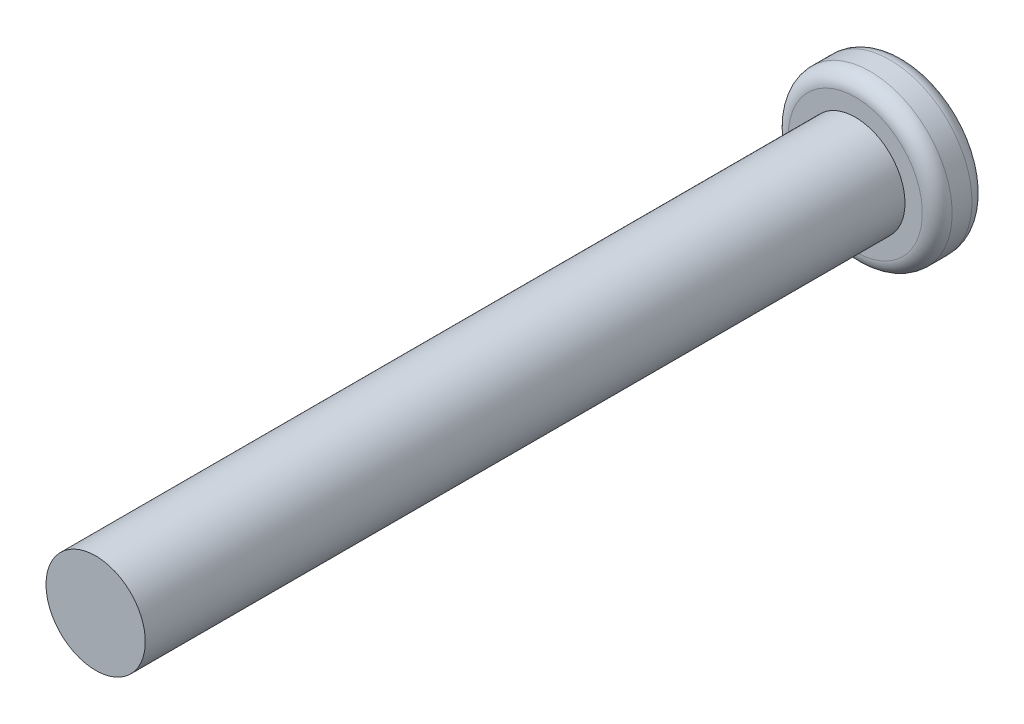
SolidWorks part; units mm, degrees
ref_plane "Front Plane" through (0, 0, 0) normal (0, 0, 1) x (1, 0, 0)
ref_plane "Top Plane" through (0, 0, 0) normal (0, 1, 0) x (1, 0, 0)
ref_plane "Right Plane" through (0, 0, 0) normal (1, 0, 0) x (0, 0, -1)
ref_plane "Plane1" through (0, 0, 0) normal (0, -1, 0) x (1, 0, 0)
sketch "Sketch1" plane through (0, 0, 0) normal (0, -1, 0) x (1, 0, 0)
  line L0 (10, 223) -> (0, 223)
  line L1 (0, 223) -> (0, 63)
  line L2 (0, 63) -> (10, 63)
  line L3 (13, 60) -> (13.5, 60)
  line L4 (16.5, 63) -> (16.5, 67)
  line L5 (13.5, 70) -> (10, 70)
  line L6 (10, 70) -> (10, 223)
  line L7 (0, 223) -> (0, 60) construction
  arc A0 (10, 63) -> (13, 60) centre (13, 63) ccw
  arc A1 (13.5, 60) -> (16.5, 63) centre (13.5, 63) ccw
  arc A2 (16.5, 67) -> (13.5, 70) centre (13.5, 67) ccw
revolve "Revolve1" add sketch "Sketch1" angle 360 about L7
